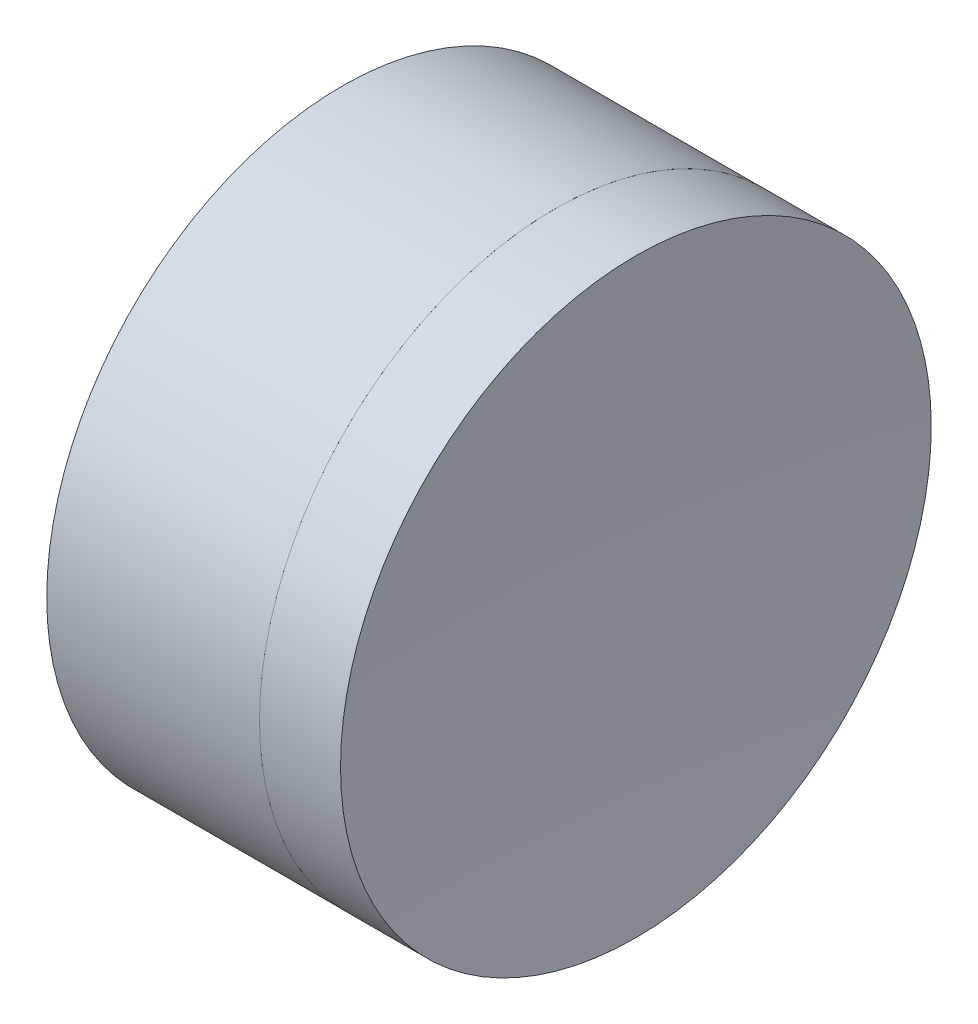
SolidWorks part; units mm, degrees
ref_plane "前视基准面" through (0, 0, 0) normal (0, 0, 1) x (1, 0, 0)
ref_plane "上视基准面" through (0, 0, 0) normal (0, 1, 0) x (1, 0, 0)
ref_plane "右视基准面" through (0, 0, 0) normal (1, 0, 0) x (0, 0, -1)
sketch "草图1" plane through (0, 0, 0) normal (0, 1, 0) x (1, 0, 0)
  line L0 (-0.8161, 0) -> (433.6173, 0) construction
  line L1 (228.3139, 6.35) -> (232.8878, 6.35)
  line L4 (228.3139, -6.35) -> (232.8878, -6.35)
  arc A0 (228.3139, -6.35) -> (228.3139, 6.35) centre (216.4006, 0) ccw
  arc A1 (232.8878, 6.35) -> (232.8878, -6.35) centre (245.7006, 0) ccw
  point P6 (229.9006, 0)
  point P8 (231.4006, 0)
  dimension "D3" = 6.35
  dimension "D4" = 1.5
  dimension "D1" = 13.5
  dimension "D5" = 14.3
  dimension "D2" = 6.35
revolve "旋转1" add sketch "草图1" angle 360 about L0
sketch "草图2" plane through (0, 0, 0) normal (0, 1, 0) x (1, 0, 0)
  line L2 (228.3139, 0) -> (234.9944, 0) construction
  line L3 (228.3139, -6.35) -> (228.3139, 6.35) construction
  line L6 (232.8878, 6.35) -> (234.6303, 6.35)
  line L7 (232.8878, -6.35) -> (234.6303, -6.35)
  arc A2 (232.8878, 6.35) -> (232.8878, -6.35) centre (245.7006, 0) ccw construction
  arc A3 (232.8878, 6.35) -> (232.8878, -6.35) centre (245.7006, 0) ccw
  arc A4 (234.6303, 6.35) -> (234.6303, -6.35) centre (322.3006, 0) ccw
  point P8 (231.4006, 0)
  point P9 (234.4006, 0)
  dimension "D1" = 3
  dimension "D2" = 87.9
revolve "旋转3" add sketch "草图2" angle 360 about L2
